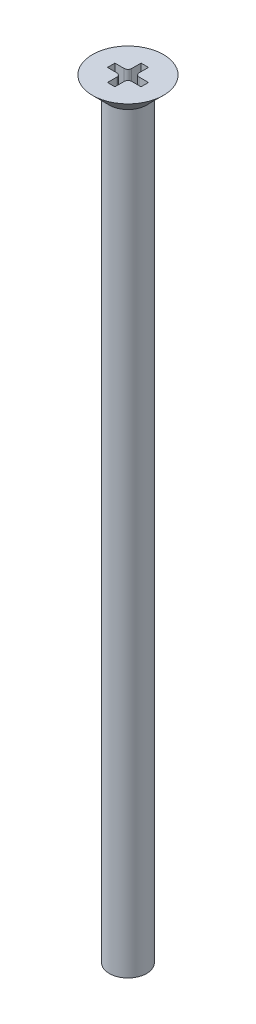
SolidWorks part; units mm, degrees
material "1023 Carbon Steel Sheet (SS)"
ref_plane "Front Plane" through (0, 0, 0) normal (0, 0, 1) x (1, 0, 0)
ref_plane "Top Plane" through (0, 0, 0) normal (0, 1, 0) x (1, 0, 0)
ref_plane "Right Plane" through (0, 0, 0) normal (1, 0, 0) x (0, 0, -1)
sketch "Sketch1" plane through (0, 0, 0) normal (1, 0, 0) x (0, 0, -1)
  line L0 (-1.9, 0) -> (1.9, 0) construction
  line L1 (-1.9, 0) -> (-1, -0.9) construction
  line L2 (-1, -0.9) -> (1, -0.9) construction
  line L3 (1, -0.9) -> (1.9, 0) construction
  line L4 (-1, -0.9) -> (-1, -1.2) construction
  line L5 (1, -0.9) -> (1, -1.2) construction
  line L6 (1, -1.2) -> (-1, -1.2) construction
  line L7 (0, 0.8723) -> (0, -0.1883) construction
  line L8 (0, 0) -> (-1.9, 0)
  line L9 (-1.9, 0) -> (-1, -0.9)
  line L10 (-1, -0.9) -> (-1, -1.2)
  line L11 (-1, -1.2) -> (0, -1.2)
  line L12 (0, 0) -> (0, -1.2)
  point P3 (0, -0.9)
  dimension "D1" = 3.8
  dimension "D2" = 90
  dimension "D3" = 2
  dimension "D4" = 1.2
revolve "Revolve1" add sketch "Sketch1" angle 360 about L7
sketch "Sketch2" plane through (0, -1.2, 0) normal (0, -1, 0) x (1, 0, 0)
  circle A0 centre (0, 0) radius 1
  dimension "D1" = 2
extrude "Boss-Extrude1" add sketch "Sketch2" along normal blind 40
sketch "Sketch3" plane through (0, 0, 0) normal (0, 1, 0) x (1, 0, 0)
  line L1 (-0.9, -0.2) -> (-0.4, -0.2)
  line L2 (-0.9, -0.2) -> (-0.9, 0.2)
  line L3 (-0.9, 0.2) -> (-0.4, 0.2)
  line L4 (0.9, -0.2) -> (0.9, 0.2)
  line L5 (-0.9, -0.2) -> (0.9, 0.2) construction
  line L6 (-0.9, 0.2) -> (0.9, -0.2) construction
  line L7 (-0.2, -0.9) -> (0.2, -0.9)
  line L8 (-0.2, -0.9) -> (-0.2, -0.4)
  line L9 (-0.2, 0.9) -> (0.2, 0.9)
  line L10 (0.2, -0.9) -> (0.2, -0.4)
  line L11 (-0.2, -0.9) -> (0.2, 0.9) construction
  line L12 (-0.2, 0.9) -> (0.2, -0.9) construction
  line L13 (-0.2, 0.4) -> (-0.2, 0.9)
  line L14 (0.4, 0.2) -> (0.9, 0.2)
  line L15 (0.2, 0.4) -> (0.2, 0.9)
  line L17 (0.4, -0.2) -> (0.9, -0.2)
  arc A0 (-0.4, 0.2) -> (-0.2, 0.4) centre (-0.4, 0.4) ccw
  arc A1 (0.2, 0.4) -> (0.4, 0.2) centre (0.4, 0.4) ccw
  arc A2 (0.4, -0.2) -> (0.2, -0.4) centre (0.4, -0.4) ccw
  arc A3 (-0.2, -0.4) -> (-0.4, -0.2) centre (-0.4, -0.4) ccw
  point P0 (0, 0)
  point P6 (0, 0)
  point P14 (-0.2, 0.2)
  point P19 (0.2, 0.2)
  point P23 (0.2, -0.2)
  dimension "D5" = 0.2
  dimension "D1" = 0.4
  dimension "D2" = 1.8
  dimension "D3" = 0.4
  dimension "D4" = 1.8
extrude "Cut-Extrude1" cut sketch "Sketch3" against normal blind 1
